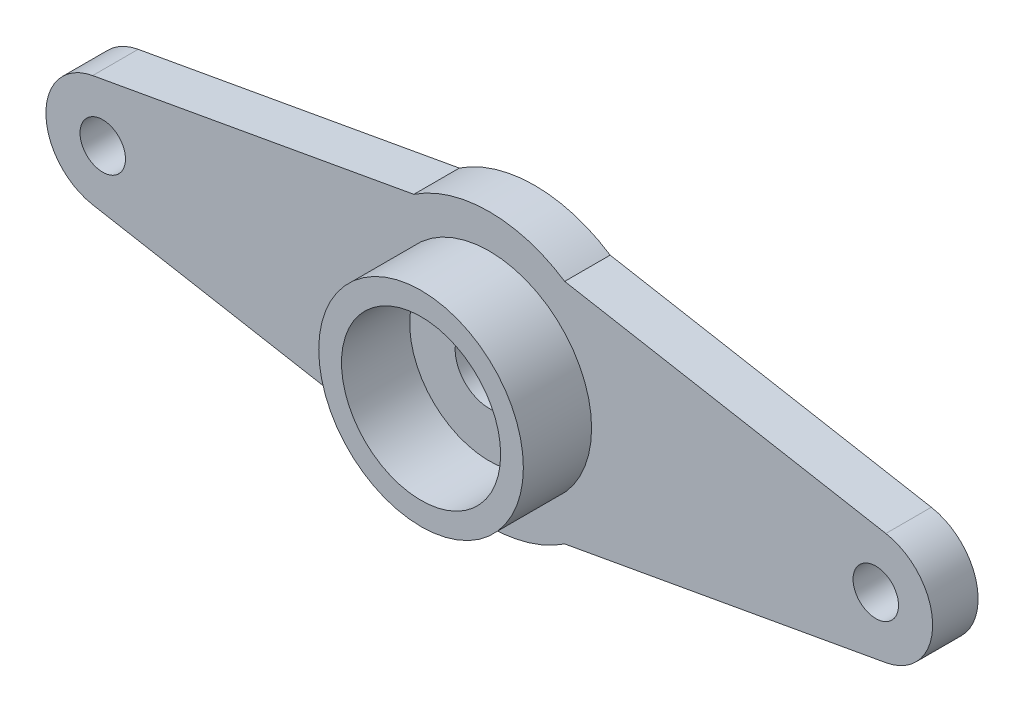
SolidWorks part; units mm, degrees
ref_plane "Front Plane" through (0, 0, 0) normal (0, 0, 1) x (1, 0, 0)
ref_plane "Top Plane" through (0, 0, 0) normal (0, 1, 0) x (1, 0, 0)
ref_plane "Right Plane" through (0, 0, 0) normal (1, 0, 0) x (0, 0, -1)
sketch "Sketch1" plane through (0, 0, 0) normal (0, 0, 1) x (1, 0, 0)
  line L0 (-17, 0) -> (17, 0) construction
  line L1 (-17.4423, 2.4606) -> (-3.3166, 5)
  line L2 (-17.4423, -2.4606) -> (-3.3166, -5)
  line L3 (3.3166, -5) -> (17.4423, -2.4606)
  line L4 (17.4423, 2.4606) -> (3.3166, 5)
  line L5 (-3.3166, 5) -> (3.3166, 5) construction
  line L6 (3.3166, 5) -> (3.3166, -5) construction
  line L7 (3.3166, -5) -> (-3.3166, -5) construction
  line L8 (-3.3166, -5) -> (-3.3166, 5) construction
  arc A0 (-3.3166, -5) -> (3.3166, -5) centre (0, 0) ccw
  arc A1 (17.4423, -2.4606) -> (17.4423, 2.4606) centre (17, 0) ccw
  arc A2 (-17.4423, 2.4606) -> (-17.4423, -2.4606) centre (-17, 0) ccw
  arc A3 (3.3166, 5) -> (-3.3166, 5) centre (0, 0) ccw
  circle A4 centre (0, 0) radius 1.5
  dimension "D1" = 12
  dimension "D2" = 5
  dimension "D5" = 3
  dimension "D3" = 34
  dimension "D4" = 10
extrude "Boss-Extrude1" add sketch "Sketch1" along normal blind 2
sketch "Sketch2" plane through (0, 0, 2) normal (0, 0, 1) x (1, 0, 0)
  circle A0 centre (0, 0) radius 4.5
  circle A1 centre (0, 0) radius 3.5
  point P5 (0, -0.0084)
  dimension "D1" = 9
  dimension "D2" = 7
extrude "Boss-Extrude2" add sketch "Sketch2" along normal blind 3
sketch "Sketch3" plane through (0, 0, 2) normal (0, 0, 1) x (1, 0, 0)
  line L0 (-17, 0) -> (17, 0) construction
  circle A0 centre (-17, 0) radius 1
  circle A1 centre (17, 0) radius 1
  dimension "D2" = 2
  dimension "D1" = 34
extrude "Cut-Extrude1" cut sketch "Sketch3" against normal through all
